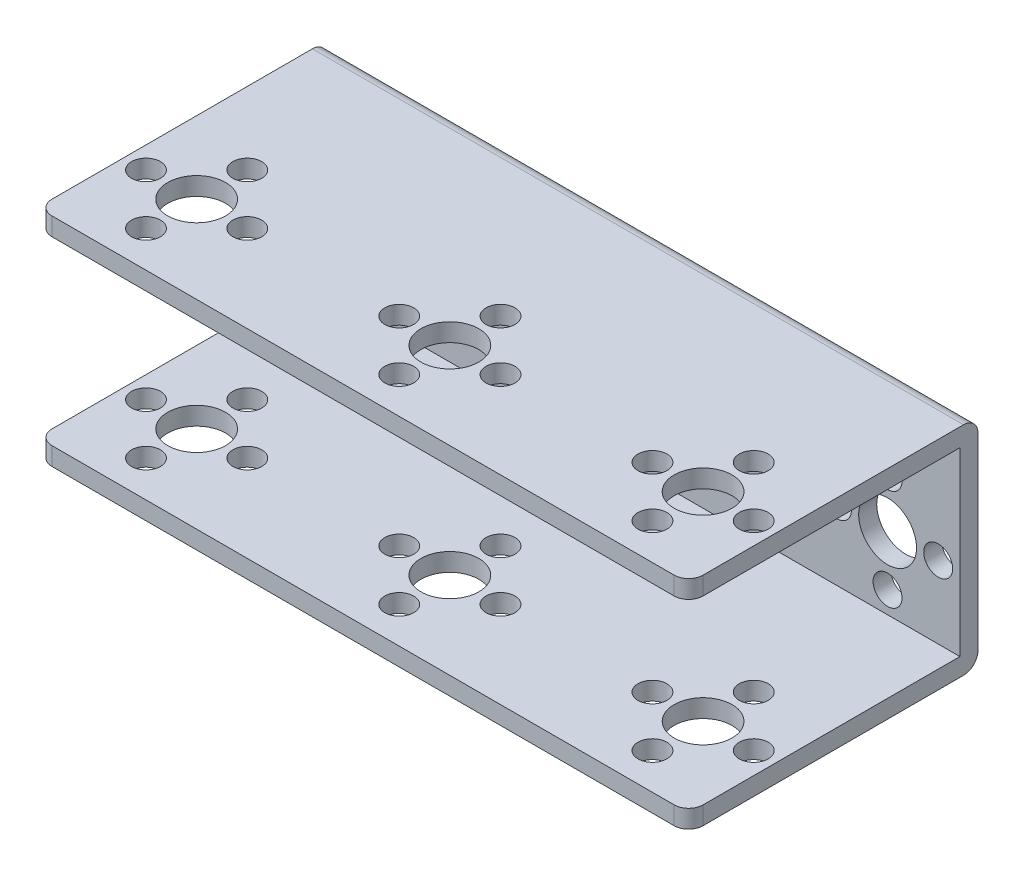
SolidWorks part; units mm, degrees
material "可锻铸铁"
ref_plane "前视基准面" through (0, 0, 0) normal (0, 0, 1) x (1, 0, 0)
ref_plane "上视基准面" through (0, 0, 0) normal (0, 1, 0) x (1, 0, 0)
ref_plane "右视基准面" through (0, 0, 0) normal (1, 0, 0) x (0, 0, -1)
sketch "草图1" plane through (0, 0, 0) normal (0, 1, 0) x (1, 0, 0)
  line L1 (-45, 20) -> (45, 20)
  line L2 (-45, 20) -> (-45, -20)
  line L3 (-45, -20) -> (45, -20)
  line L4 (45, 20) -> (45, -20)
  line L5 (-45, 20) -> (45, -20) construction
  line L6 (-45, -20) -> (45, 20) construction
  point P0 (0, 0)
  dimension "D1" = 40
  dimension "D2" = 90
extrude "凸台-拉伸1" add sketch "草图1" along normal blind 30
ref_plane "基准面4" through (0, 0, 20) normal (0, 0, 1) x (1, 0, 0)
sketch "草图2" plane through (0, 0, 20) normal (0, 0, 1) x (1, 0, 0)
  line L1 (45, 30) -> (45, 0) construction
  line L2 (-45, 27.5) -> (45, 27.5)
  line L3 (-45, 27.5) -> (-45, 2.5)
  line L4 (-45, 2.5) -> (45, 2.5)
  line L5 (45, 27.5) -> (45, 2.5)
  point P4 (0, 15)
  dimension "D1" = 25
  dimension "D2" = 90
extrude "切除-拉伸1" cut sketch "草图2" against normal blind 37.5
ref_plane "基准面5" through (0, 15, 0) normal (0, -1, 0) x (-1, 0, 0)
ref_plane "基准面6" through (0, 30, 0) normal (0, 1, 0) x (1, 0, 0)
sketch "草图3" plane through (0, 30, 0) normal (0, 1, 0) x (1, 0, 0)
  line L5 (-1.375, -20) -> (1.375, -20) construction
  line L6 (45, -20) -> (45, 20) construction
  circle A0 centre (35, -8) radius 4
  circle A1 centre (42, -8) radius 2
  circle A2 centre (35, -15) radius 2
  circle A3 centre (28, -8) radius 2
  circle A4 centre (35, -1) radius 2
  circle A5 centre (0, -8) radius 4
  circle A6 centre (-7, -8) radius 2
  circle A7 centre (0, -1) radius 2
  circle A8 centre (0, -15) radius 2
  circle A9 centre (7, -8) radius 2
  circle A10 centre (-35, -8) radius 4
  circle A11 centre (-42, -8) radius 2
  circle A12 centre (-35, -1) radius 2
  circle A13 centre (-35, -15) radius 2
  circle A14 centre (-28, -8) radius 2
  point P0 (0, 0)
  dimension "D3" = 8
  dimension "D4" = 4
  dimension "D1" = 12
  dimension "D2" = 10
  dimension "D5" = 7
  dimension "D6" = 3
  dimension "D8" = 3
  dimension "D7" = 4
extrude "切除-拉伸2" cut sketch "草图3" against normal up to next (2.5 mm away)
mirror "镜向1" about plane through (0, 15, 0) normal (0, -1, 0) of "切除-拉伸2"
sketch "草图4" plane through (0, 0, -20) normal (0, 0, -1) x (-1, 0, 0)
  line L0 (45, 30) -> (45, 0) construction
  line L2 (-45, 0) -> (45, 0) construction
  circle A0 centre (35, 12.5) radius 4
  circle A1 centre (42, 12.5) radius 2
  circle A2 centre (35, 5.5) radius 2
  circle A3 centre (28, 12.5) radius 2
  circle A4 centre (35, 19.5) radius 2
  circle A5 centre (7, 12.5) radius 2
  circle A6 centre (0, 12.5) radius 4
  circle A7 centre (-7, 12.5) radius 2
  circle A8 centre (0, 5.5) radius 2
  circle A9 centre (0, 19.5) radius 2
  circle A10 centre (-28, 12.5) radius 2
  circle A11 centre (-35, 12.5) radius 4
  circle A12 centre (-42, 12.5) radius 2
  circle A13 centre (-35, 5.5) radius 2
  circle A14 centre (-35, 19.5) radius 2
  dimension "D2" = 8
  dimension "D3" = 4
  dimension "D1" = 10
  dimension "D4" = 7
  dimension "D5" = 12.5
  dimension "D6" = 12.5
  dimension "D8" = 3
  dimension "D7" = 4
extrude "切除-拉伸3" cut sketch "草图4" against normal up to next
fillet "圆角1" radius 2 1 edges at (-45, 28.75, 20)
fillet "圆角2" radius 2 1 edges at (45, 28.75, 20)
fillet "圆角3" radius 2 1 edges at (45, 1.25, 20)
fillet "圆角4" radius 2 1 edges at (-45, 1.25, 20)
fillet "圆角5" radius 2 1 edges at (0, 0, -20)
fillet "圆角6" radius 2 1 edges at (0, 30, -20)
